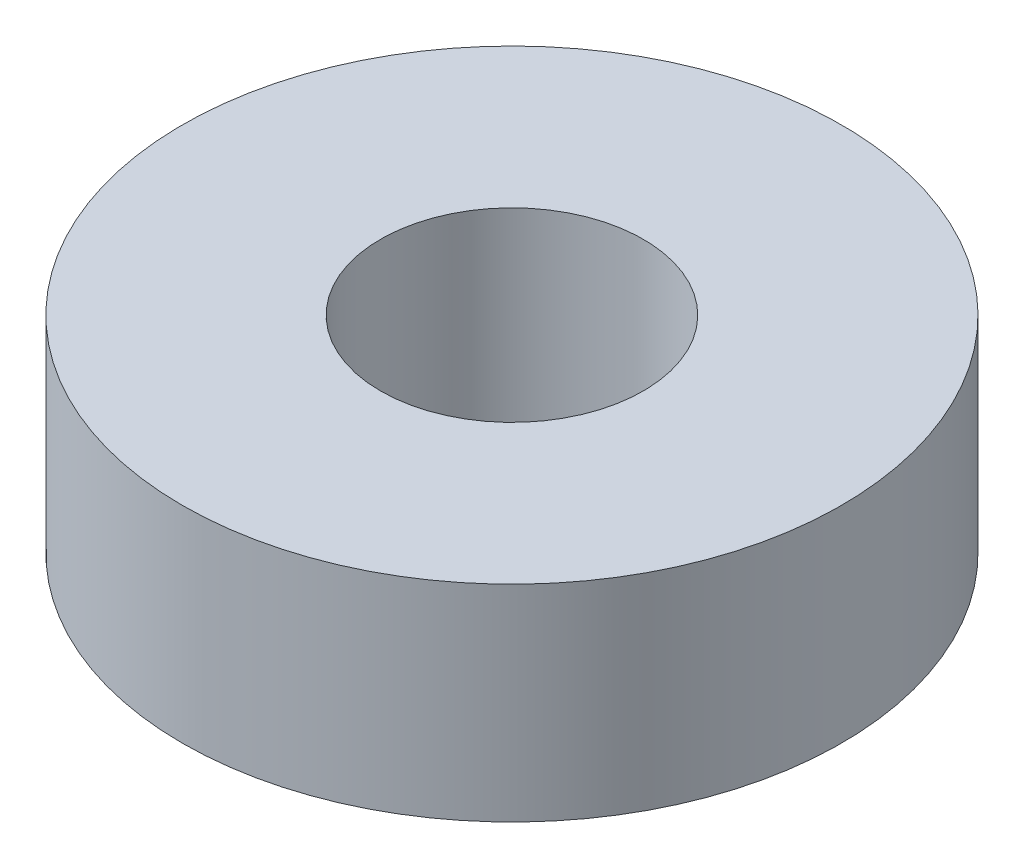
SolidWorks part; units mm, degrees
ref_plane "Front Plane" through (0, 0, 0) normal (0, 0, 1) x (1, 0, 0)
ref_plane "Top Plane" through (0, 0, 0) normal (0, 1, 0) x (1, 0, 0)
ref_plane "Right Plane" through (0, 0, 0) normal (1, 0, 0) x (0, 0, -1)
sketch "Sketch1" plane through (0, 0, 0) normal (0, 1, 0) x (1, 0, 0)
  circle A0 centre (0, 0) radius 8
extrude "Boss-Extrude1" add sketch "Sketch1" along normal blind 5 contours A0
sketch "Sketch2" plane through (0, 0, 0) normal (0, 1, 0) x (1, 0, 0)
  circle A0 centre (0, 0) radius 3.19
extrude "Cut-Extrude1" cut sketch "Sketch2" along normal blind 5
